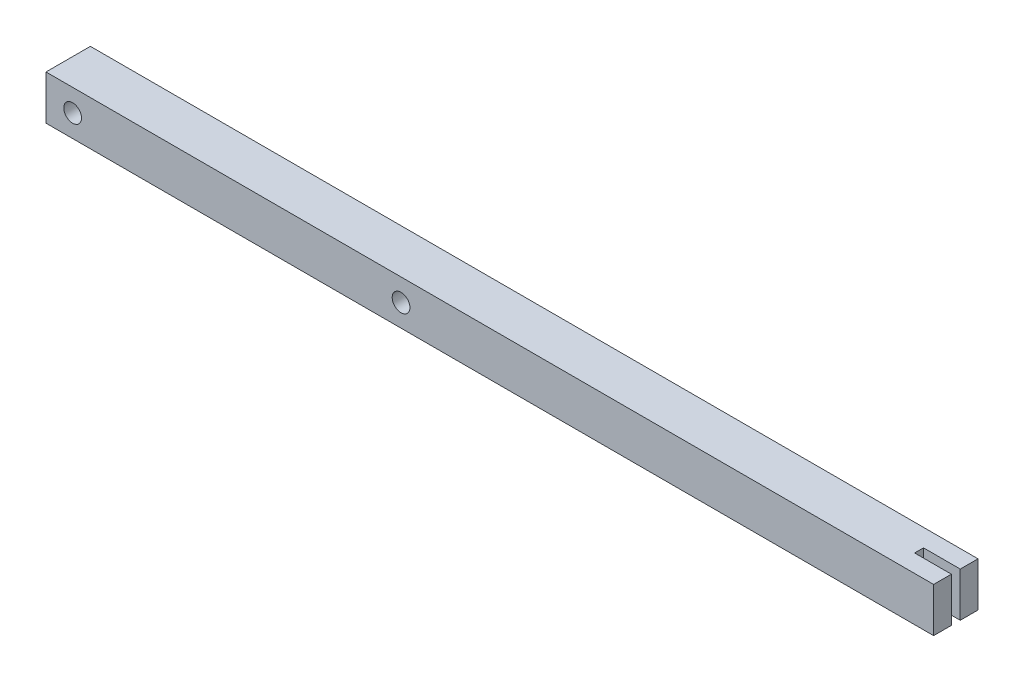
SolidWorks part; units mm, degrees
ref_plane "Front Plane" through (0, 0, 0) normal (0, 0, 1) x (1, 0, 0)
ref_plane "Top Plane" through (0, 0, 0) normal (0, 1, 0) x (1, 0, 0)
ref_plane "Right Plane" through (0, 0, 0) normal (1, 0, 0) x (0, 0, -1)
sketch "Sketch1" plane through (0, 0, 0) normal (0, 1, 0) x (1, 0, 0)
  line L1 (250, -12.5) -> (-250, -12.5)
  line L2 (250, -12.5) -> (250, 12.5)
  line L3 (250, 12.5) -> (-250, 12.5)
  line L4 (-250, -12.5) -> (-250, 12.5)
  line L5 (250, -12.5) -> (-250, 12.5) construction
  line L6 (250, 12.5) -> (-250, -12.5) construction
  point P0 (0, 0)
extrude "Boss-Extrude1" add sketch "Sketch1" along normal blind 25
sketch "Sketch2" plane through (0, 0, 12.5) normal (0, 0, 1) x (1, 0, 0)
  circle A0 centre (-235, 12.5) radius 5
  circle A1 centre (-50, 12.5) radius 5
extrude "Cut-Extrude1" cut sketch "Sketch2" against normal blind 25
sketch "Sketch5" plane through (0, 25, 0) normal (0, 1, 0) x (1, 0, 0)
  line L0 (229.2958, -2.5) -> (250.0458, -2.5)
  line L1 (229.2958, -2.5) -> (229.2958, 2.5)
  line L2 (250.0458, -2.5) -> (250.0458, 2.5)
  line L3 (229.2958, 2.5) -> (250.0458, 2.5)
  line L4 (229.2958, -2.5) -> (250.0458, 2.5) construction
  line L5 (250.0458, -2.5) -> (229.2958, 2.5) construction
  point P1 (239.6708, 0)
extrude "Cut-Extrude2" cut sketch "Sketch5" against normal blind 25
